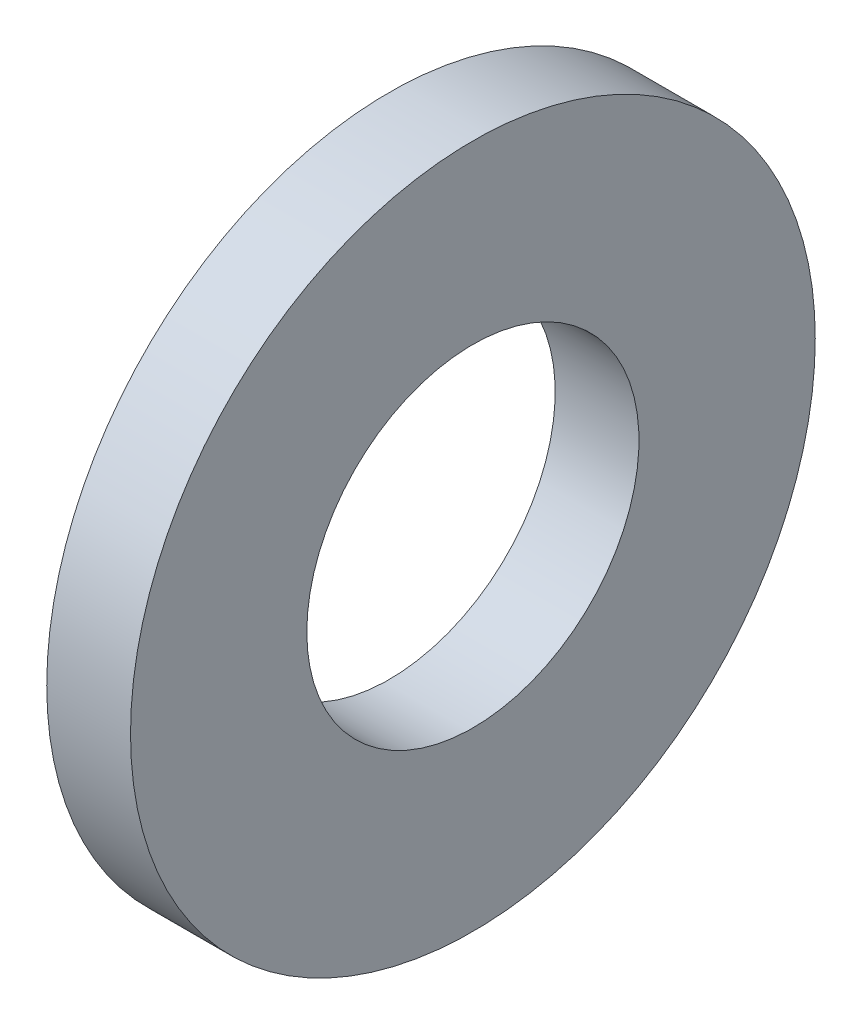
SolidWorks part; units mm, degrees
ref_plane "Plane1" through (0, 0, 0) normal (0, 0, 1) x (1, 0, 0)
ref_plane "Plane2" through (0, 0, 0) normal (0, 1, 0) x (1, 0, 0)
ref_plane "Plane3" through (0, 0, 0) normal (1, 0, 0) x (0, 0, -1)
sketch "Sketch1" plane through (0, 0, 0) normal (0, 0, 1) x (1, 0, 0)
  line L0 (-34.925, 0) -> (9.525, 0) construction
  line L1 (0, 4.56) -> (0, 9.4)
  line L2 (0, 9.4) -> (-2.3, 9.4)
  line L3 (-2.3, 9.4) -> (-2.3, 4.56)
  line L4 (-2.3, 4.56) -> (0, 4.56)
  dimension "Thickness" = 2.3
  dimension "Inside_dia" = 9.12
  dimension "Outside_dia" = 18.8
revolve "Base-Revolve" add sketch "Sketch1" angle 360 about L0
